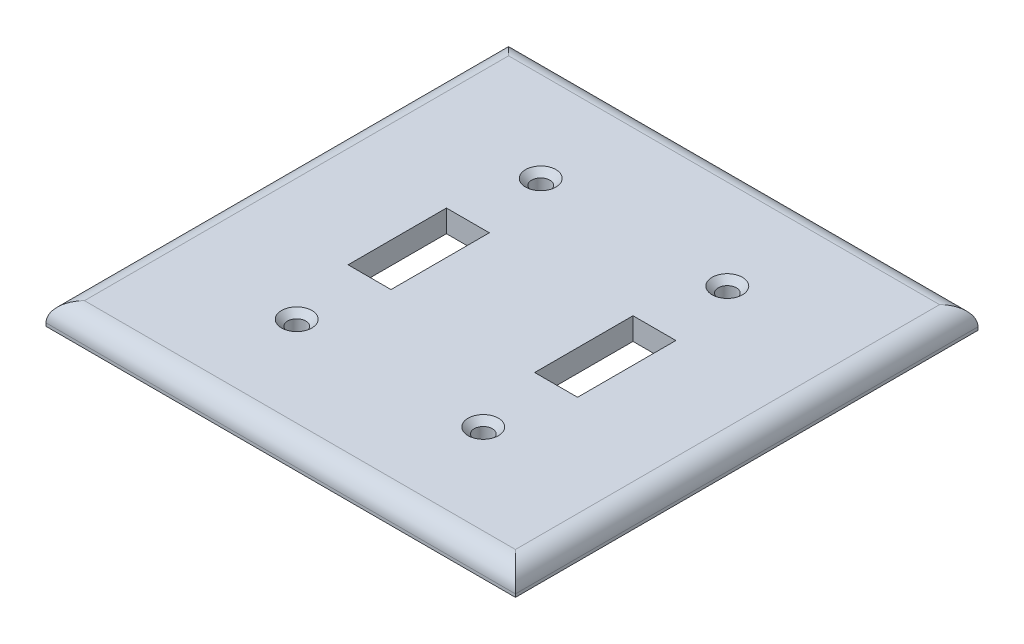
SolidWorks part; units mm, degrees
ref_plane "Front" through (0, 0, 0) normal (0, 0, 1) x (1, 0, 0)
ref_plane "Top" through (0, 0, 0) normal (0, 1, 0) x (1, 0, 0)
ref_plane "Right" through (0, 0, 0) normal (1, 0, 0) x (0, 0, -1)
sketch "Sketch1" plane through (0, 0, 0) normal (0, 1, 0) x (1, 0, 0)
  line L0 (-26.0746, 6.3229) -> (-26.0746, 24.3229)
  line L1 (-61.0246, 51.3229) -> (54.9754, 51.3229)
  line L2 (-61.0246, 51.3229) -> (-61.0246, -62.9771)
  line L3 (-61.0246, -62.9771) -> (54.9754, -62.9771)
  line L4 (54.9754, 51.3229) -> (54.9754, -62.9771)
  line L5 (-31.3746, 6.3229) -> (-20.7746, 6.3229)
  line L6 (-31.3746, 6.3229) -> (-31.3746, -17.9771)
  line L7 (-31.3746, -17.9771) -> (-20.7746, -17.9771)
  line L8 (-20.7746, 6.3229) -> (-20.7746, -17.9771)
  line L9 (14.7254, 6.3229) -> (25.3254, 6.3229)
  line L10 (14.7254, 6.3229) -> (14.7254, -17.9771)
  line L11 (14.7254, -17.9771) -> (25.3254, -17.9771)
  line L12 (25.3254, 6.3229) -> (25.3254, -17.9771)
  line L13 (-26.0746, -17.9771) -> (-26.0746, -35.9771)
  line L14 (20.0254, -17.9771) -> (20.0254, -35.9771)
  line L15 (20.0254, 6.3229) -> (20.0254, 24.3229)
  circle A0 centre (-26.0746, 24.3229) radius 2.25
  circle A1 centre (-26.0746, -35.9771) radius 2.25
  circle A2 centre (20.0254, -35.9771) radius 2.25
  circle A3 centre (20.0254, 24.3229) radius 2.25
  dimension "D10" = 4.5
  dimension "D1" = 116
  dimension "D2" = 114.3
  dimension "D3" = 10.6
  dimension "D4" = 24.3
  dimension "D5" = 45
  dimension "D6" = 29.65
  dimension "D7" = 29.65
  dimension "D8" = 45
  dimension "D9" = 18
extrude "Boss-Extrude1" add sketch "Sketch1" along normal blind 5.5 contours L4 L1 L2 L3 L5 L8 L7 L6 L9 L12 L11 L10 | L8 L5 L6 L7
fillet "Fillet1" radius 4.75 4 edges at (-61.0246, 5.5, 5.8271) (-3.0246, 5.5, 62.9771) (54.9754, 5.5, 5.8271) (-3.0246, 5.5, -51.3229)
chamfer "Chamfer1" distance 1.5 angle 45 4 edges at (20.0254, 5.5, 38.2271) (-26.0746, 5.5, 38.2271) (20.0254, 5.5, -22.0729) (-26.0746, 5.5, -22.0729)
